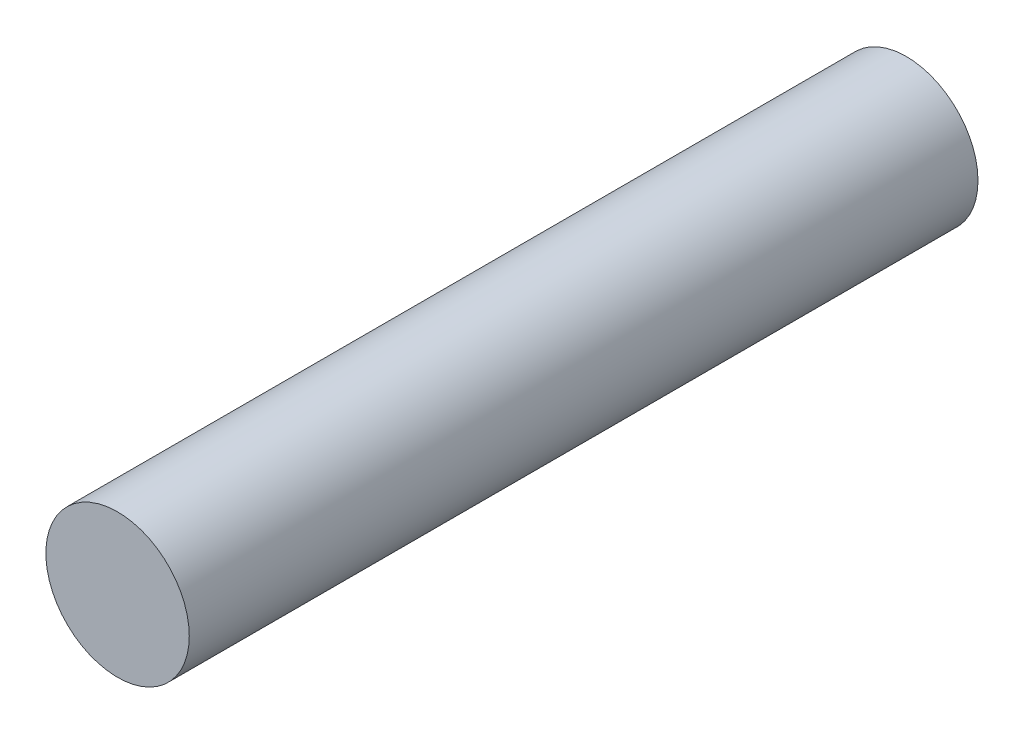
SolidWorks part; units mm, degrees
ref_plane "Alzado" through (0, 0, 0) normal (0, 0, 1) x (1, 0, 0)
ref_plane "Planta" through (0, 0, 0) normal (0, 1, 0) x (1, 0, 0)
ref_plane "Vista lateral" through (0, 0, 0) normal (1, 0, 0) x (0, 0, -1)
sketch "Croquis1" plane through (0, 0, 0) normal (0, 0, 1) x (1, 0, 0)
  circle A0 centre (0, 0) radius 0.25
  dimension "D1" = 0.5
extrude "Saliente-Extruir1" add sketch "Croquis1" along normal blind 2.75
